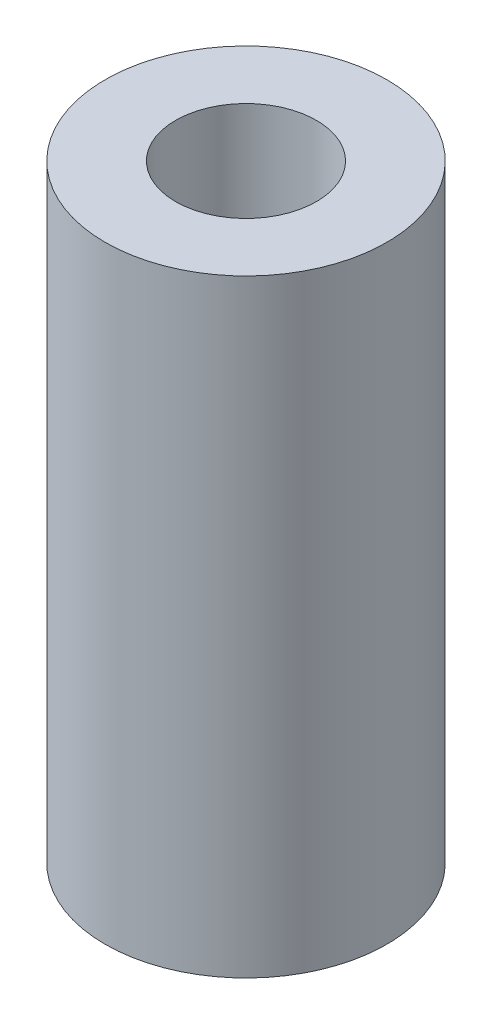
SolidWorks part; units mm, degrees
material "Delrin 2700 NC010, Low Viscosity Acetal Copolymer (SS)"
ref_plane "Front Plane" through (0, 0, 0) normal (0, 0, 1) x (1, 0, 0)
ref_plane "Top Plane" through (0, 0, 0) normal (0, 1, 0) x (1, 0, 0)
ref_plane "Right Plane" through (0, 0, 0) normal (1, 0, 0) x (0, 0, -1)
sketch "Sketch1" plane through (0, 0, 0) normal (0, 1, 0) x (1, 0, 0)
  circle A0 centre (0, 0) radius 1.5
  circle A1 centre (0, 0) radius 3
  dimension "D1" = 3
  dimension "D2" = 1.5
extrude "Boss-Extrude1" add sketch "Sketch1" along normal mid plane 12.948
